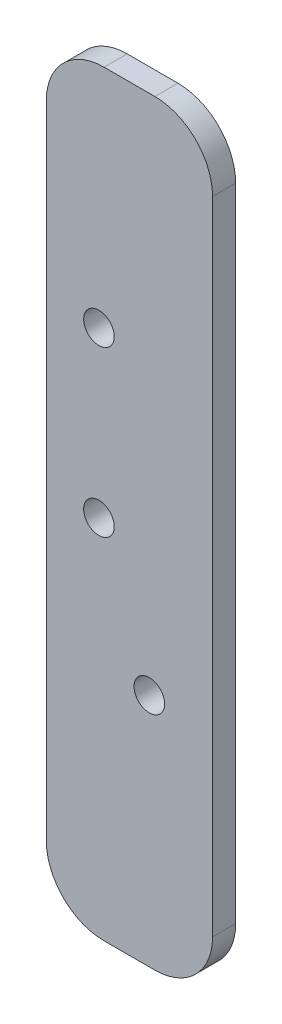
SolidWorks part; units mm, degrees
ref_plane "Front Plane" through (0, 0, 0) normal (0, 0, 1) x (1, 0, 0)
ref_plane "Top Plane" through (0, 0, 0) normal (0, 1, 0) x (1, 0, 0)
ref_plane "Right Plane" through (0, 0, 0) normal (1, 0, 0) x (0, 0, -1)
sketch "Sketch1" plane through (0, 0, 0) normal (0, 0, 1) x (1, 0, 0)
  line L1 (-63.2759, -253.8551) -> (-34.4731, -253.8551)
  line L2 (-63.2759, -253.8551) -> (-63.2759, -384.9337)
  line L3 (-63.2759, -384.9337) -> (-34.4731, -384.9337)
  line L4 (-34.4731, -253.8551) -> (-34.4731, -384.9337)
extrude "Boss-Extrude1" add sketch "Sketch1" along normal blind 4
hole_wizard "M5 Clearance Hole1" positions "Sketch4" profile "Sketch2" hole size "M5" standard "ISO" end condition through all
sketch "Sketch4" plane through (0, 0, 4) normal (0, 0, 1) x (1, 0, 0)
  point P0 (-54.1627, -321.9157)
  point P2 (-54.1627, -293.4157)
sketch "Sketch2" plane through (-54.1627, -321.9157, 4) normal (1, 0, 0) x (0, -1, 0)
  line L0 (0, 0) -> (0, 4)
  line L1 (0, 4) -> (2.65, 4)
  line L2 (2.65, 4) -> (2.65, 0)
  line L5 (2.65, 0) -> (0, 0)
  line L11 (0, -6.35) -> (0, 107.95) construction
  dimension "Thru Hole Dia." = 5.3
  dimension "Thru Hole Depth" = 4
fillet "Fillet1" radius 10 4 edges at (-63.2759, -253.8551, 2) (-34.4731, -253.8551, 2) (-63.2759, -384.9337, 2) (-34.4731, -384.9337, 2)
hole_wizard "M5 Clearance Hole2" positions "Sketch6" profile "Sketch5" hole size "M5" standard "ISO" end condition through all
sketch "Sketch6" plane through (0, 0, 0) normal (0, 0, -1) x (-1, 0, 0)
  point P0 (45.4264, -344.1655)
sketch "Sketch5" plane through (-45.4264, -344.1655, 0) normal (1, 0, 0) x (0, 1, 0)
  line L0 (0, 0) -> (0, 4)
  line L1 (0, 4) -> (2.65, 4)
  line L2 (2.65, 4) -> (2.65, 0)
  line L5 (2.65, 0) -> (0, 0)
  line L11 (0, -6.35) -> (0, 107.95) construction
  dimension "Thru Hole Dia." = 5.3
  dimension "Thru Hole Depth" = 4
